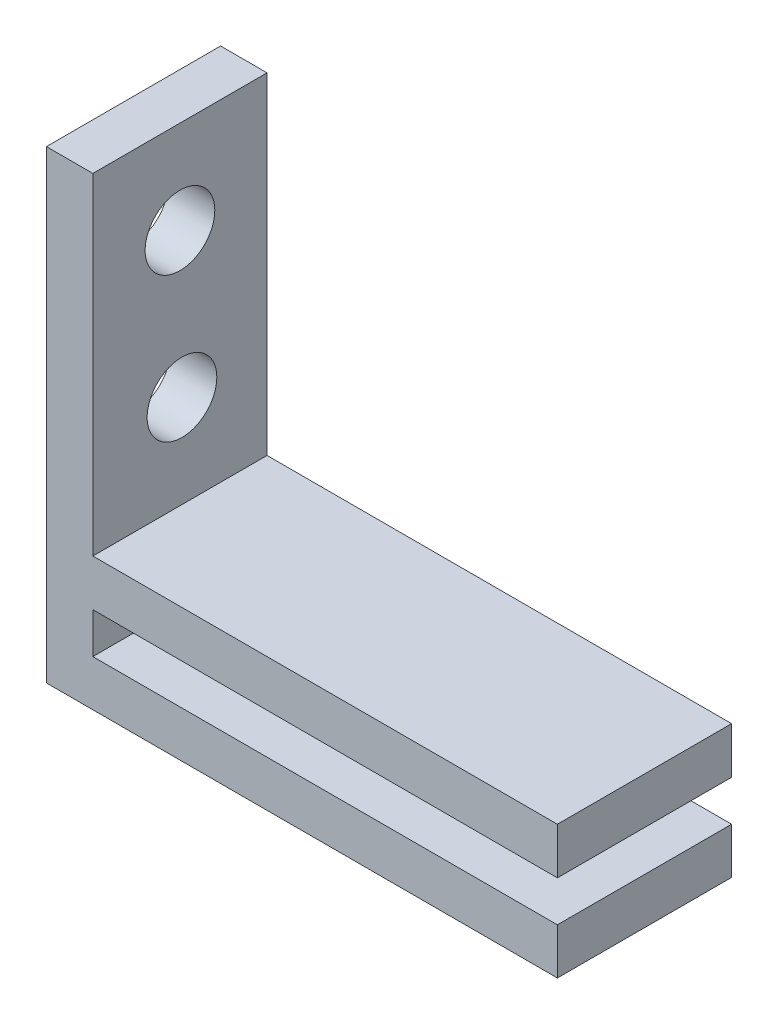
SolidWorks part; units mm, degrees
ref_plane "Front Plane" through (0, 0, 0) normal (0, 0, 1) x (1, 0, 0)
ref_plane "Top Plane" through (0, 0, 0) normal (0, 1, 0) x (1, 0, 0)
ref_plane "Right Plane" through (0, 0, 0) normal (1, 0, 0) x (0, 0, -1)
sketch "Sketch1" plane through (0, 0, 0) normal (1, 0, 0) x (0, 0, -1)
  line L1 (-0.7404, 9.0244) -> (6.7596, 9.0244)
  line L2 (-0.7404, 9.0244) -> (-0.7404, -10.9756)
  line L3 (-0.7404, -10.9756) -> (6.7596, -10.9756)
  line L4 (6.7596, 9.0244) -> (6.7596, -10.9756)
  dimension "D1" = 20
  dimension "D2" = 7.5
extrude "Boss-Extrude2" add sketch "Sketch1" along normal blind 2
sketch "Sketch2" plane through (2, 0, 0) normal (1, 0, 0) x (0, 0, -1)
  line L0 (-0.7404, 9.0244) -> (-0.7404, -10.9756) construction
  line L1 (6.7596, -10.9756) -> (-0.7404, -10.9756)
  line L2 (6.7596, -10.9756) -> (6.7596, -8.9921)
  line L3 (6.7596, -8.9921) -> (-0.7404, -8.9921)
  line L4 (-0.7404, -10.9756) -> (-0.7404, -8.9921)
extrude "Boss-Extrude3" add sketch "Sketch2" along normal blind 20
sketch "Sketch3" plane through (2, 0, 0) normal (1, 0, 0) x (0, 0, -1)
  line L0 (6.7596, -8.9921) -> (6.7596, 9.0244) construction
  line L1 (-0.7404, -8.9921) -> (6.7596, -8.9921)
  line L2 (-0.7404, -8.9921) -> (-0.7404, -7.2421)
  line L3 (-0.7404, -7.2421) -> (6.7596, -7.2421)
  line L4 (6.7596, -8.9921) -> (6.7596, -7.2421)
  line L6 (-0.7404, -7.2421) -> (6.7596, -7.2421)
  line L7 (-0.7404, -7.2421) -> (-0.7404, -5.2421)
  line L8 (-0.7404, -5.2421) -> (6.7596, -5.2421)
  line L9 (6.7596, -7.2421) -> (6.7596, -5.2421)
  line M5 (6.7596, -8.9921) -> (6.7596, 9.0244)
  line M7 (-0.7404, 9.0244) -> (-0.7404, -8.9921)
  dimension "D1" = 2
  dimension "D2" = 1.75
extrude "Boss-Extrude4" add sketch "Sketch3" along normal blind 20 contours L8 L3 M7 M5
sketch "Sketch5" plane through (2, 0, 0) normal (1, 0, 0) x (0, 0, -1)
  line L0 (6.7596, -5.2421) -> (6.7596, 9.0244) construction
  line L2 (6.7596, 9.0244) -> (-0.7404, 9.0244) construction
  line L5 (-0.7404, -5.2421) -> (6.7596, -5.2421) construction
  circle A0 centre (3.0096, 5.0244) radius 1.5
  circle A1 centre (3.0965, -1.2421) radius 1.5
  dimension "D1" = 3.75
  dimension "D2" = 4
  dimension "D3" = 4
extrude "Cut-Extrude1" cut sketch "Sketch5" against normal blind 20
sketch "Sketch6" plane through (0, -5.2421, 0) normal (0, 1, 0) x (1, 0, 0)
  line L0 (22, 6.7596) -> (2, 6.7596) construction
  line L1 (2, -0.7404) -> (2, 6.7596) construction
  circle A0 centre (14, 3.0096) radius 1.6
  dimension "D1" = 3.75
  dimension "D2" = 12
